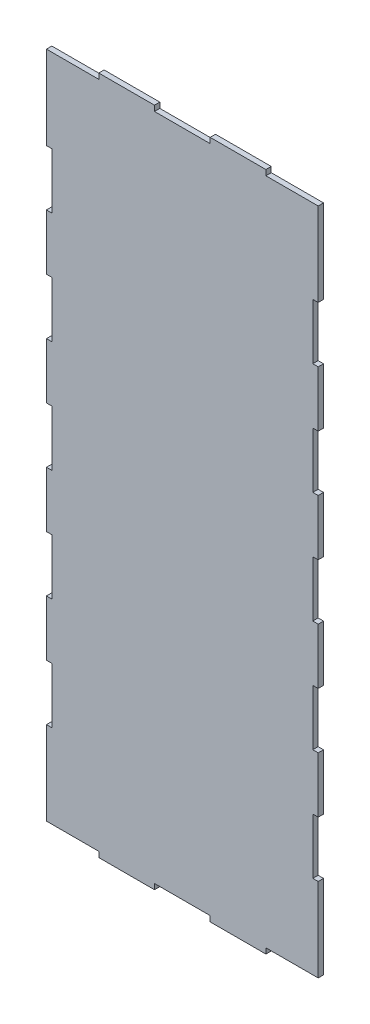
SolidWorks part; units mm, degrees
ref_plane "Front Plane" through (0, 0, 0) normal (0, 0, 1) x (1, 0, 0)
ref_plane "Top Plane" through (0, 0, 0) normal (0, 1, 0) x (1, 0, 0)
ref_plane "Right Plane" through (0, 0, 0) normal (1, 0, 0) x (0, 0, -1)
sketch "Sketch1" plane through (0, 0, 0) normal (0, 0, 1) x (1, 0, 0)
  line B0 (0, 6238.8694) -> (0, 5457.8194)
  line B1 (0, 5457.8194) -> (50.8, 5457.8194)
  line B2 (50.8, 5457.8194) -> (50.8, 4937.1194)
  line B3 (50.8, 4937.1194) -> (0, 4937.1194)
  line B4 (0, 4937.1194) -> (0, 4416.4194)
  line B5 (0, 4416.4194) -> (50.8, 4416.4194)
  line B6 (50.8, 4416.4194) -> (50.8, 3895.7194)
  line B7 (50.8, 3895.7194) -> (0, 3895.7194)
  line B8 (0, 3895.7194) -> (0, 3375.0194)
  line B9 (0, 3375.0194) -> (50.8, 3375.0194)
  line B10 (50.8, 3375.0194) -> (50.8, 2854.3194)
  line B11 (50.8, 2854.3194) -> (0, 2854.3194)
  line B12 (0, 2854.3194) -> (0, 2333.6194)
  line B13 (0, 2333.6194) -> (50.8, 2333.6194)
  line B14 (50.8, 2333.6194) -> (50.8, 1812.9194)
  line B15 (50.8, 1812.9194) -> (0, 1812.9194)
  line B16 (0, 1812.9194) -> (0, 1292.2194)
  line B17 (0, 1292.2194) -> (50.8, 1292.2194)
  line B18 (50.8, 1292.2194) -> (50.8, 771.5194)
  line B19 (50.8, 771.5194) -> (0, 771.5194)
  line B20 (0, 771.5194) -> (0, 250.8194)
  line B21 (0, 250.8194) -> (0, -9.5306)
  line B22 (0, -9.5306) -> (488.95, -9.5306)
  line B23 (488.95, -9.5306) -> (488.95, -60.3306)
  line B24 (488.95, -60.3306) -> (1009.65, -60.3306)
  line B25 (1009.65, -60.3306) -> (1009.65, -9.5306)
  line B26 (1009.65, -9.5306) -> (1530.35, -9.5306)
  line B27 (1530.35, -9.5306) -> (1530.35, -60.3306)
  line B28 (1530.35, -60.3306) -> (2051.05, -60.3306)
  line B29 (2051.05, -60.3306) -> (2051.05, -9.5306)
  line B30 (2051.05, -9.5306) -> (2540, -9.5306)
  line B31 (2540, -9.5306) -> (2540, 771.5194)
  line B32 (2540, 771.5194) -> (2489.2, 771.5194)
  line B33 (2489.2, 771.5194) -> (2489.2, 1292.2194)
  line B34 (2489.2, 1292.2194) -> (2540, 1292.2194)
  line B35 (2540, 1292.2194) -> (2540, 1812.9194)
  line B36 (2540, 1812.9194) -> (2489.2, 1812.9194)
  line B37 (2489.2, 1812.9194) -> (2489.2, 2333.6194)
  line B38 (2489.2, 2333.6194) -> (2540, 2333.6194)
  line B39 (2540, 2333.6194) -> (2540, 2854.3194)
  line B40 (2540, 2854.3194) -> (2489.2, 2854.3194)
  line B41 (2489.2, 2854.3194) -> (2489.2, 3375.0194)
  line B42 (2489.2, 3375.0194) -> (2540, 3375.0194)
  line B43 (2540, 3375.0194) -> (2540, 3895.7194)
  line B44 (2540, 3895.7194) -> (2489.2, 3895.7194)
  line B45 (2489.2, 3895.7194) -> (2489.2, 4416.4194)
  line B46 (2489.2, 4416.4194) -> (2540, 4416.4194)
  line B47 (2540, 4416.4194) -> (2540, 4937.1194)
  line B48 (2540, 4937.1194) -> (2489.2, 4937.1194)
  line B49 (2489.2, 4937.1194) -> (2489.2, 5457.8194)
  line B50 (2489.2, 5457.8194) -> (2540, 5457.8194)
  line B51 (2540, 5457.8194) -> (2540, 5978.5194)
  line B52 (2540, 5978.5194) -> (2540, 6238.8694)
  line B53 (2540, 6238.8694) -> (2051.05, 6238.8694)
  line B54 (2051.05, 6238.8694) -> (2051.05, 6289.6694)
  line B55 (2051.05, 6289.6694) -> (1530.35, 6289.6694)
  line B56 (1530.35, 6289.6694) -> (1530.35, 6238.8694)
  line B57 (1530.35, 6238.8694) -> (1009.65, 6238.8694)
  line B58 (1009.65, 6238.8694) -> (1009.65, 6289.6694)
  line B59 (1009.65, 6289.6694) -> (488.95, 6289.6694)
  line B60 (488.95, 6289.6694) -> (488.95, 6238.8694)
  line B61 (488.95, 6238.8694) -> (0, 6238.8694)
sketch_block_instance "s4-1"
sketch_block "s4"
extrude "Boss-Extrude1" add sketch "Sketch1" along normal blind 50
scale "Scale1" scale about centroid uniform scaling yes scale factor 0.04
